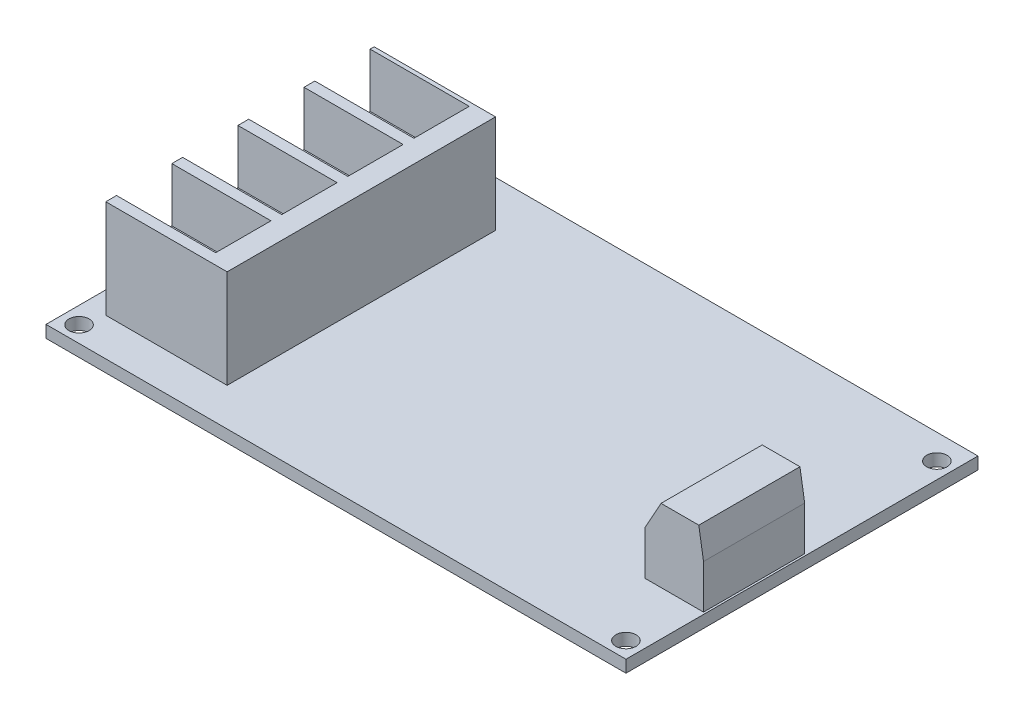
SolidWorks part; units mm, degrees
ref_plane "Front Plane" through (0, 0, 0) normal (0, 0, 1) x (1, 0, 0)
ref_plane "Top Plane" through (0, 0, 0) normal (0, 1, 0) x (1, 0, 0)
ref_plane "Right Plane" through (0, 0, 0) normal (1, 0, 0) x (0, 0, -1)
sketch "Sketch1" plane through (0, 0, 0) normal (0, 1, 0) x (1, 0, 0)
  line L1 (0, 0) -> (86, 0)
  line L2 (0, 0) -> (0, 52.2)
  line L3 (0, 52.2) -> (86, 52.2)
  line L4 (86, 0) -> (86, 52.2)
  dimension "D1" = 52.2
  dimension "D2" = 86
extrude "Boss-Extrude1" add sketch "Sketch1" along normal blind 1.8
sketch "Sketch3" plane through (0, 1.8, 0) normal (0, 1, 0) x (1, 0, 0)
  line L0 (86, 0) -> (86, 52.2) construction
  line L1 (0, 0) -> (86, 0) construction
  circle A0 centre (83.6, 2.4) radius 1.5
  circle A1 centre (83.6, 48.5) radius 1.5
  circle A2 centre (2.5, 2.4) radius 1.5
  circle A3 centre (2.5, 48.5) radius 1.5
  point P4 (0, 0)
  point P11 (0, 0)
  point P14 (0, 0)
  point P15 (0, 0)
  point P16 (0, 0)
  dimension "D1" = 3
  dimension "D4" = 3
  dimension "D6" = 3
  dimension "D8" = 3
  dimension "D2" = 2.4
  dimension "D3" = 2.4
  dimension "D5" = 48.5
  dimension "D7" = 83.5
extrude "Cut-Extrude1" cut sketch "Sketch3" against normal blind 1.8
sketch "Sketch4" plane through (0, 1.8, 0) normal (0, 1, 0) x (1, 0, 0)
  line L0 (0, 0) -> (86, 0) construction
  line L1 (77, 26.8) -> (85.7, 26.8)
  line L2 (77, 26.8) -> (77, 11.8)
  line L3 (77, 11.8) -> (85.7, 11.8)
  line L4 (85.7, 26.8) -> (85.7, 11.8)
  line L5 (86, 0) -> (86, 52.2) construction
  dimension "D1" = 15
  dimension "D2" = 8.7
  dimension "D3" = 26.8
  dimension "D4" = 9
extrude "Boss-Extrude2" add sketch "Sketch4" along normal blind 6.5 separate body
sketch "Sketch5" plane through (0, 8.3, 0) normal (0, 1, 0) x (1, 0, 0)
  line L0 (85.7, 26.8) -> (77, 26.8) construction
  line L1 (79.4, 26.8) -> (85, 26.8)
  line L2 (79.4, 26.8) -> (79.4, 11.8)
  line L3 (79.4, 11.8) -> (85, 11.8)
  line L4 (85, 26.8) -> (85, 11.8)
  line L5 (85.7, 11.8) -> (85.7, 26.8) construction
  dimension "D1" = 15
  dimension "D2" = 5.6
  dimension "D3" = 0.7
extrude "Boss-Extrude3" add sketch "Sketch5" along normal blind 4.32
ref_plane "Plane1" through (0, 0, -19.3) normal (0, 0, 1) x (1, 0, 0)
sketch "Sketch7" plane through (0, 0, -19.3) normal (0, 0, 1) x (1, 0, 0)
  line L0 (79.4, 12.62) -> (77, 8.3)
rib "Rib11" sketch "Sketch7" sketch "Sketch7" thickness 15 extrusion direction parallel to sketch draft on no parameters "D1"=15
sketch "Sketch8" plane through (0, 0, -19.3) normal (0, 0, 1) x (1, 0, 0)
  line L0 (85, 12.62) -> (85.7, 8.3)
rib "Rib14" sketch "Sketch8" sketch "Sketch8" thickness 15 extrusion direction parallel to sketch draft on no parameters "D1"=15
sketch "Sketch9" plane through (0, 1.8, 0) normal (0, 1, 0) x (1, 0, 0)
  line L0 (0, 0) -> (86, 0) construction
  line L1 (3.26, 45.4) -> (21.26, 45.4)
  line L2 (3.26, 45.4) -> (3.26, 5.6)
  line L3 (3.26, 5.6) -> (21.26, 5.6)
  line L4 (21.26, 45.4) -> (21.26, 5.6)
  line L5 (86, 0) -> (86, 52.2) construction
  dimension "D1" = 18
  dimension "D2" = 39.8
  dimension "D3" = 45.4
  dimension "D4" = 82.74
extrude "Boss-Extrude4" add sketch "Sketch9" along normal blind 14.58 separate body
sketch "Sketch10" plane through (0, 16.38, 0) normal (0, 1, 0) x (1, 0, 0)
  line L0 (3.26, 45.4) -> (3.26, 5.6) construction
  line L1 (3.26, 7.2) -> (17.96, 7.2)
  line L2 (3.26, 7.2) -> (3.26, 15.4)
  line L3 (3.26, 15.4) -> (17.96, 15.4)
  line L4 (17.96, 7.2) -> (17.96, 15.4)
  line L5 (21.26, 5.6) -> (21.26, 45.4) construction
  line L6 (3.26, 5.6) -> (21.26, 5.6) construction
  line L7 (3.26, 17) -> (3.26, 25.2)
  line L8 (3.26, 17) -> (17.96, 17)
  line L9 (17.96, 17) -> (17.96, 25.2)
  line L10 (3.26, 25.2) -> (17.96, 25.2)
  line L11 (3.26, 26.8) -> (3.26, 35)
  line L12 (3.26, 26.8) -> (17.96, 26.8)
  line L13 (17.96, 26.8) -> (17.96, 35)
  line L14 (3.26, 35) -> (17.96, 35)
  line L15 (3.26, 36.6) -> (3.26, 44.8)
  line L16 (3.26, 36.6) -> (17.96, 36.6)
  line L17 (17.96, 36.6) -> (17.96, 44.8)
  line L18 (3.26, 44.8) -> (17.96, 44.8)
  dimension "D1" = 3.3
  dimension "D2" = 1.6
  dimension "D3" = 8.2
  dimension "D5" = 1.6
  dimension "D4" = 4
extrude "Cut-Extrude2" cut sketch "Sketch10" against normal blind 8
